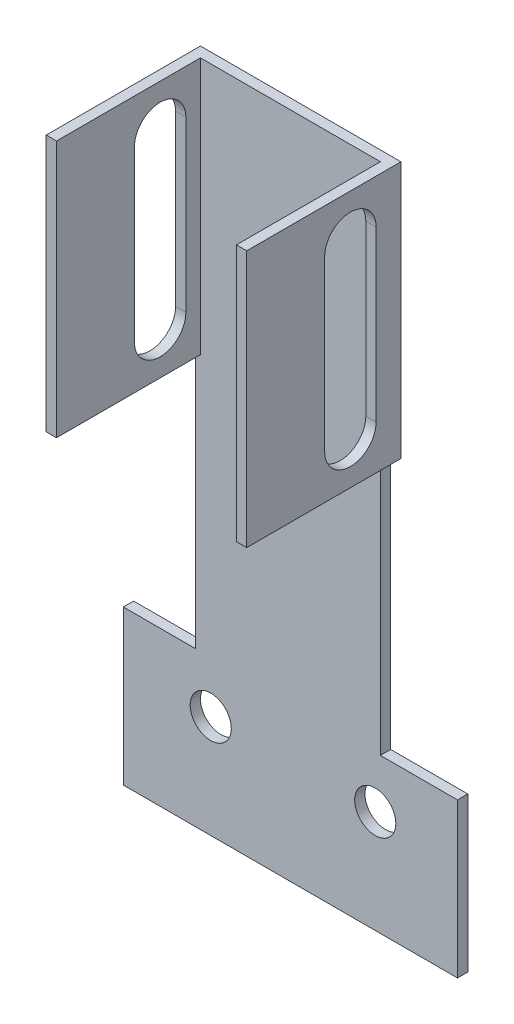
SolidWorks part; units mm, degrees
ref_plane "前视基准面" through (0, 0, 0) normal (0, 0, 1) x (1, 0, 0)
ref_plane "上视基准面" through (0, 0, 0) normal (0, 1, 0) x (1, 0, 0)
ref_plane "右视基准面" through (0, 0, 0) normal (1, 0, 0) x (0, 0, -1)
sketch "草图1" plane through (0, 0, 0) normal (0, 0, 1) x (1, 0, 0)
  line L0 (-27.5308, -16.07) -> (37.4692, -16.07)
  line L1 (37.4692, -16.07) -> (37.4692, 13.93)
  line L2 (37.4692, 13.93) -> (22.4692, 13.93)
  line L3 (22.4692, 13.93) -> (22.4692, 113.93)
  line L4 (-27.5308, -16.07) -> (-27.5308, 13.93)
  line L5 (-27.5308, 13.93) -> (-13.5308, 13.93)
  line L6 (-13.5308, 13.93) -> (-13.5308, 113.93)
  line L7 (-13.5308, 113.93) -> (22.4692, 113.93)
  line L8 (37.4692, 13.93) -> (37.4692, 3.93) construction
  line L9 (37.4692, 3.93) -> (21.4692, 3.93) construction
  line L10 (21.4692, 3.93) -> (-10.5308, 3.93) construction
  circle A0 centre (21.4692, 3.93) radius 4
  circle A1 centre (-10.5308, 3.93) radius 4
  dimension "D9" = 8
  dimension "D10" = 8
  dimension "D1" = 65
  dimension "D2" = 30
  dimension "D3" = 15
  dimension "D4" = 100
  dimension "D5" = 14
  dimension "D6" = 10
  dimension "D7" = 16
  dimension "D8" = 32
extrude "凸台-拉伸1" add sketch "草图1" along normal blind 2
sketch "草图2" plane through (22.4692, 0, 0) normal (1, 0, 0) x (0, 0, -1)
  line L0 (0, 113.93) -> (0, 63.93)
  line L1 (0, 13.93) -> (0, 113.93) construction
  line L2 (0, 63.93) -> (-30, 63.93)
  line L3 (-30, 63.93) -> (-30, 113.93)
  line L4 (-30, 113.93) -> (0, 113.93)
  dimension "D1" = 30
extrude "凸台-拉伸2" add sketch "草图2" along normal blind 2
ref_plane "基准面1" through (4.9692, 0, 0) normal (1, 0, 0) x (0, 0, -1)
mirror "镜向1" about plane through (4.9692, 0, 0) normal (1, 0, 0) of "凸台-拉伸2"
sketch "草图3" plane through (24.4692, 0, 0) normal (1, 0, 0) x (0, 0, -1)
  line L1 (0, 113.93) -> (-30, 113.93) construction
  line L2 (-30, 63.93) -> (0, 63.93) construction
  line L3 (-15, 113.93) -> (-9.8374, 105.3657) construction
  line L4 (-15, 63.93) -> (-9.8374, 72.4943) construction
  line L5 (-14.8374, 105.3657) -> (-14.8374, 72.4943)
  line L6 (-4.8374, 105.3657) -> (-4.8374, 72.4943)
  line L7 (-9.8374, 72.4943) -> (-15, 63.93) construction
  arc A0 (-4.8374, 105.3657) -> (-14.8374, 105.3657) centre (-9.8374, 105.3657) ccw
  arc A1 (-14.8374, 72.4943) -> (-4.8374, 72.4943) centre (-9.8374, 72.4943) ccw
  dimension "D2" = 10
  dimension "D4" = 10
  dimension "D1" = 10
  dimension "D3" = 10
extrude "切除-拉伸1" cut sketch "草图3" against normal blind 55
